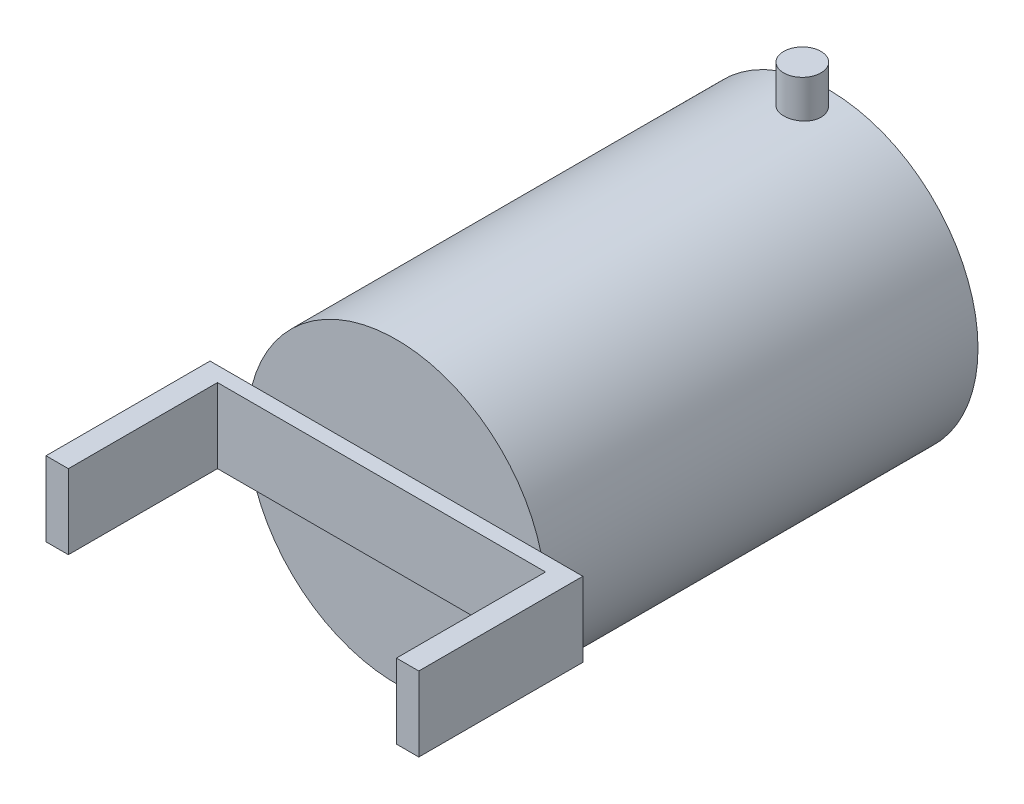
SolidWorks part; units mm, degrees
ref_plane "Front Plane" through (0, 0, 0) normal (0, 0, 1) x (1, 0, 0)
ref_plane "Top Plane" through (0, 0, 0) normal (0, 1, 0) x (1, 0, 0)
ref_plane "Right Plane" through (0, 0, 0) normal (1, 0, 0) x (0, 0, -1)
sketch "Sketch1" plane through (0, 0, 0) normal (0, 0, 1) x (1, 0, 0)
  circle A0 centre (0, 0) radius 20
  dimension "D1" = 40
extrude "Boss-Extrude1" add sketch "Sketch1" along normal blind 58
sketch "Sketch7" plane through (0, 0, 0) normal (0, 1, 0) x (1, 0, 0)
  circle A0 centre (0, -3.5617) radius 2.5
  dimension "D1" = 5
extrude "Boss-Extrude2" add sketch "Sketch7" along normal blind 25
sketch "Sketch8" plane through (0, 0, 58) normal (0, 0, 1) x (1, 0, 0)
  line L1 (-25, 5) -> (25, 5)
  line L2 (-25, 5) -> (-25, -5)
  line L3 (-25, -5) -> (25, -5)
  line L4 (25, 5) -> (25, -5)
  line L5 (-25, 5) -> (25, -5) construction
  line L6 (-25, -5) -> (25, 5) construction
  point P0 (0, 0)
  dimension "D1" = 10
  dimension "D2" = 50
extrude "Boss-Extrude3" add sketch "Sketch8" along normal blind 2
sketch "Sketch9" plane through (0, 0, 60) normal (0, 0, 1) x (1, 0, 0)
  line L0 (-25, -5) -> (25, -5) construction
  line L1 (-25, 5) -> (-22, 5)
  line L2 (-25, 5) -> (-25, -5)
  line L3 (-25, -5) -> (-22, -5)
  line L4 (-22, 5) -> (-22, -5)
  dimension "D1" = 10
  dimension "D2" = 3
extrude "Boss-Extrude4" add sketch "Sketch9" along normal blind 20
sketch "Sketch10" plane through (0, 0, 60) normal (0, 0, 1) x (1, 0, 0)
  line L0 (-22, -5) -> (25, -5) construction
  line L1 (25, 5) -> (22, 5)
  line L2 (25, 5) -> (25, -5)
  line L3 (25, -5) -> (22, -5)
  line L4 (22, 5) -> (22, -5)
  dimension "D1" = 3
extrude "Boss-Extrude5" add sketch "Sketch10" along normal blind 20
mirror "Mirror1" about plane through (0, 0, 0) normal (0, 1, 0) of "Boss-Extrude2"
